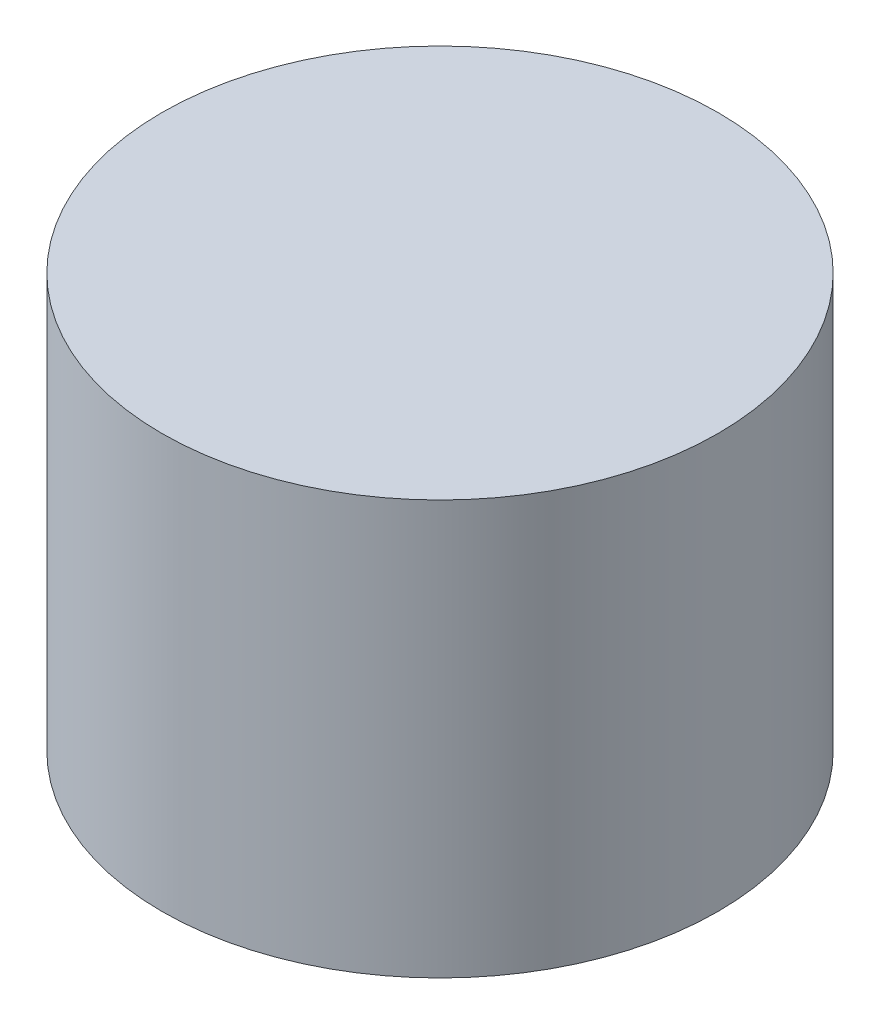
SolidWorks part; units mm, degrees
ref_plane "Alzado" through (0, 0, 0) normal (0, 0, 1) x (1, 0, 0)
ref_plane "Planta" through (0, 0, 0) normal (0, 1, 0) x (1, 0, 0)
ref_plane "Vista lateral" through (0, 0, 0) normal (1, 0, 0) x (0, 0, -1)
sketch "Croquis1" plane through (0, 0, 0) normal (0, 1, 0) x (1, 0, 0)
  circle A0 centre (0, 0) radius 45
  circle A1 centre (0, 0) radius 42.8
  dimension "D1" = 90
  dimension "D2" = 2.2
extrude "Saliente-Extruir1" add sketch "Croquis1" along normal blind 65
sketch "Croquis2" plane through (0, 65, 0) normal (0, 1, 0) x (1, 0, 0)
  circle A0 centre (0, 0) radius 45
extrude "Saliente-Extruir2" add sketch "Croquis2" along normal blind 2
